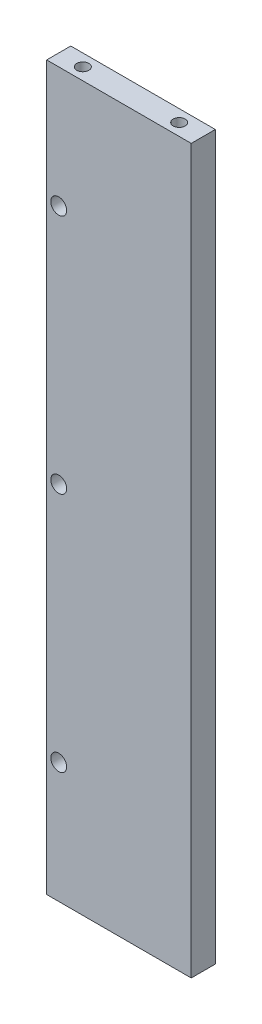
SolidWorks part; units mm, degrees
ref_plane "Front Plane" through (0, 0, 0) normal (0, 0, 1) x (1, 0, 0)
ref_plane "Top Plane" through (0, 0, 0) normal (0, 1, 0) x (1, 0, 0)
ref_plane "Right Plane" through (0, 0, 0) normal (1, 0, 0) x (0, 0, -1)
sketch "Sketch1" plane through (0, 0, 0) normal (0, 0, 1) x (1, 0, 0)
  line L1 (0, 0) -> (60, 0)
  line L2 (0, 0) -> (0, 300)
  line L3 (0, 300) -> (60, 300)
  line L4 (60, 0) -> (60, 300)
  dimension "D1" = 60
  dimension "D2" = 300
extrude "Boss-Extrude1" add sketch "Sketch1" along normal blind 10
sketch "Sketch2" plane through (0, 300, 0) normal (0, 1, 0) x (1, 0, 0)
  line L0 (60, -10) -> (60, 0) construction
  line L1 (0, -10) -> (0, 0) construction
  line L2 (60, 0) -> (0, 0) construction
  circle A0 centre (10, -5) radius 2.5
  circle A1 centre (50, -5) radius 2.5
  point P6 (60, -5)
  point P9 (0, -5)
  dimension "D1" = 5
  dimension "D2" = 5
  dimension "D3" = 10
  dimension "D4" = 10
  dimension "D5" = 5
  dimension "D6" = 5
sketch "Sketch3" plane through (0, 0, 0) normal (0, -1, 0) x (1, 0, 0)
  line L0 (0, 10) -> (0, 0) construction
  line L1 (60, 10) -> (60, 0) construction
  line L3 (0, 0) -> (60, 0) construction
  circle A0 centre (50, 5) radius 2.5
  circle A1 centre (10, 5) radius 2.5
  dimension "D1" = 5
  dimension "D2" = 5
  dimension "D3" = 10
  dimension "D4" = 5
  dimension "D5" = 5
  dimension "D6" = 10
hole_wizard "M6 Tapped Hole1" positions "Sketch6" profile "Sketch5" tap size "M6" standard "ISO"
sketch "Sketch6" plane through (0, 0, 0) normal (0, -1, 0) x (-1, 0, 0)
  point P0 (-50, -5)
  point P3 (-10, -5)
sketch "Sketch5" plane through (50, 0, 5) normal (1, 0, 0) x (0, 0, -1)
  line L0 (0, 0) -> (0, 24.5022)
  line L1 (0, 24.5022) -> (2.5, 23)
  line L2 (2.5, 23) -> (2.5, 0)
  line L5 (2.5, 0) -> (0, 0)
  line L10 (0, 24.5022) -> (-2.5, 23) construction
  line L11 (0, -6.35) -> (0, 107.95) construction
  dimension "Tap Drill Dia." = 5
  dimension "Tap Drill Depth" = 23
  dimension "Drill Angle" = 118
cosmetic thread "Hole Thread1" parameters "D1"=17, "D2"=6
cosmetic thread "Hole Thread2" parameters "D1"=17, "D2"=6
hole_wizard "M6 Tapped Hole2" positions "Sketch7" profile "Sketch8" tap size "M6" standard "ISO"
sketch "Sketch7" plane through (0, 300, 0) normal (0, 1, 0) x (1, 0, 0)
  point P0 (10, -5)
  point P3 (50, -5)
sketch "Sketch8" plane through (10, 300, 5) normal (1, 0, 0) x (0, 0, 1)
  line L0 (0, 0) -> (0, 24.5022)
  line L1 (0, 24.5022) -> (2.5, 23)
  line L2 (2.5, 23) -> (2.5, 0)
  line L5 (2.5, 0) -> (0, 0)
  line L10 (0, 24.5022) -> (-2.5, 23) construction
  line L11 (0, -6.35) -> (0, 107.95) construction
  dimension "Tap Drill Dia." = 5
  dimension "Tap Drill Depth" = 23
  dimension "Drill Angle" = 118
cosmetic thread "Hole Thread3" parameters "D1"=17, "D2"=6
cosmetic thread "Hole Thread4" parameters "D1"=17, "D2"=6
sketch "Sketch9" plane through (0, 0, 10) normal (0, 0, 1) x (1, 0, 0)
  line L0 (60, 300) -> (0, 300) construction
  line L1 (0, 0) -> (60, 0) construction
  line L2 (0, 300) -> (0, 0) construction
  circle A0 centre (5, 250) radius 3.3
  circle A2 centre (5, 50) radius 3.3
  circle A3 centre (5, 150) radius 3.5551
  point P14 (30, 0)
  dimension "D7" = 6.6
  dimension "D9" = 6.6
  dimension "D1" = 50
  dimension "D3" = 50
  dimension "D5" = 5
  dimension "D6" = 5
  dimension "D10" = 5
  dimension "D11" = 150
hole_wizard "Ø6.6 (6.6) Diameter Slot1" positions "Sketch10" profile "Sketch11" size "Ø6.6" standard "ISO" slot yes end condition through all
sketch "Sketch10" plane through (0, 0, 0) normal (0, 0, -1) x (-1, 0, 0)
  point P0 (-5, 50)
  point P3 (-5, 150)
  point P9 (-5, 250)
sketch "Sketch11" plane through (5, 50, 0) normal (1, 0, 0) x (0, 1, 0)
  line L0 (0, 0) -> (0, 10)
  line L1 (0, 10) -> (3.3, 10)
  line L2 (3.3, 10) -> (3.3, 0)
  line L5 (3.3, 0) -> (0, 0)
  line L11 (0, -6.35) -> (0, 107.95) construction
  dimension "Thru Hole Dia." = 6.6
  dimension "Thru Hole Depth" = 10
